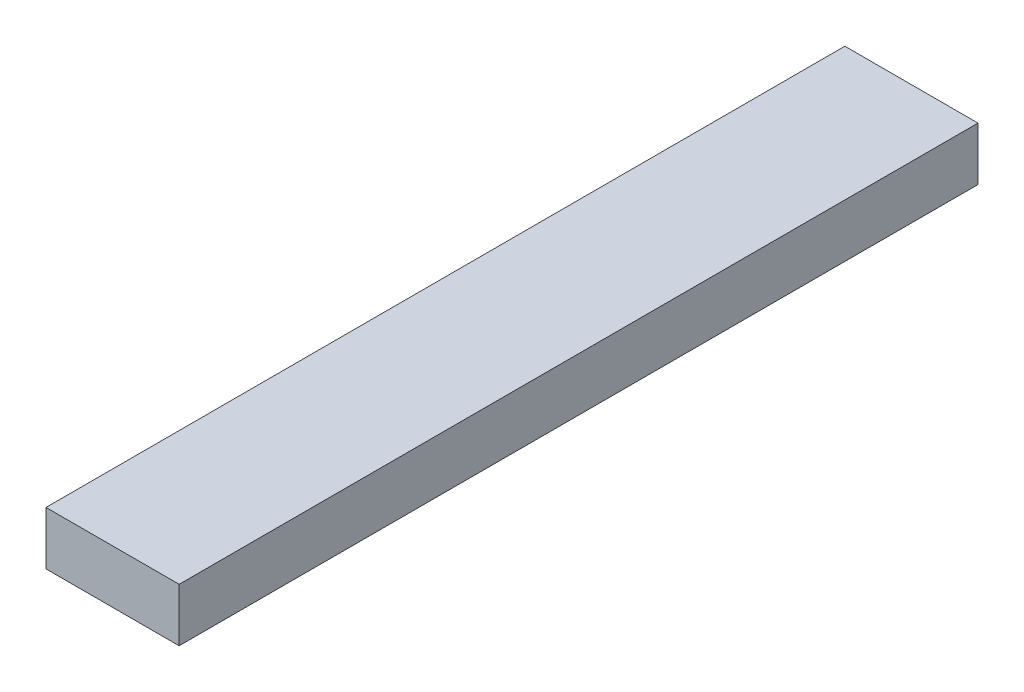
SolidWorks part; units mm, degrees
ref_plane "Front Plane" through (0, 0, 0) normal (0, 0, 1) x (1, 0, 0)
ref_plane "Top Plane" through (0, 0, 0) normal (0, 1, 0) x (1, 0, 0)
ref_plane "Right Plane" through (0, 0, 0) normal (1, 0, 0) x (0, 0, -1)
sketch "Sketch1" plane through (0, 0, 0) normal (0, 1, 0) x (1, 0, 0)
  line L1 (0, 0) -> (5, 0)
  line L2 (0, 0) -> (0, 30)
  line L3 (0, 30) -> (5, 30)
  line L4 (5, 0) -> (5, 30)
  dimension "D1" = 5
  dimension "D2" = 30
extrude "Boss-Extrude1" add sketch "Sketch1" along normal blind 2
